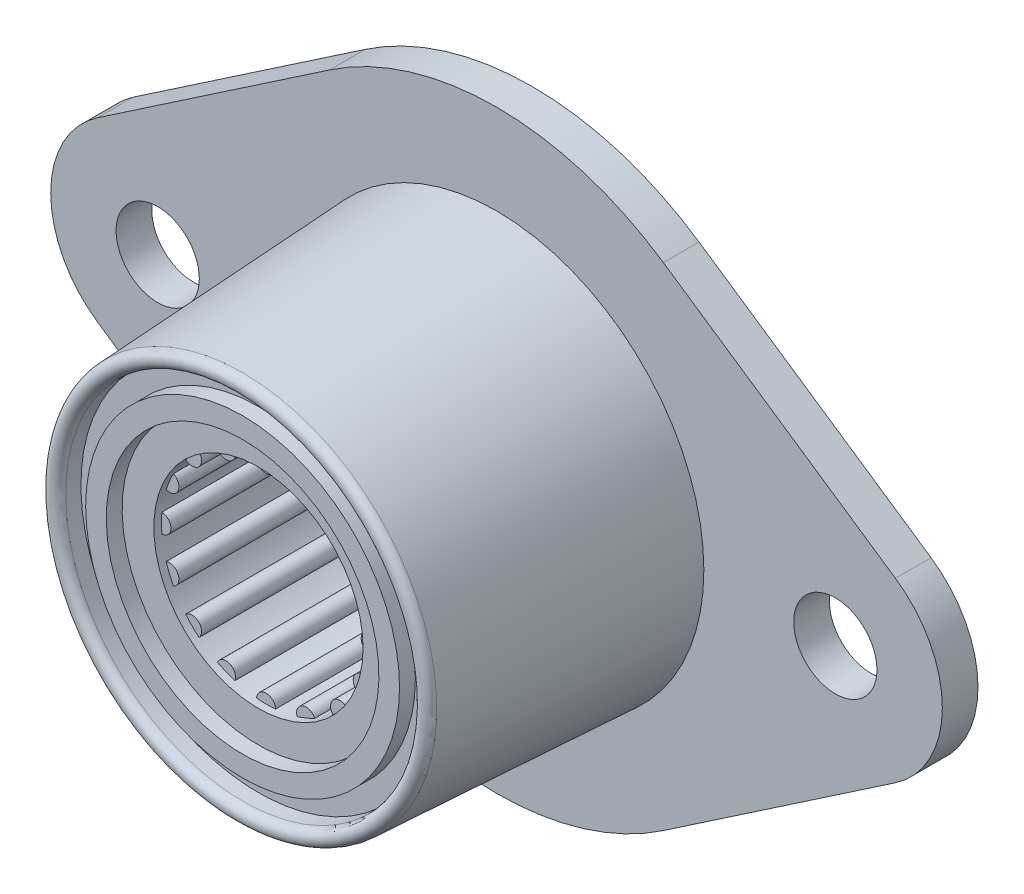
SolidWorks part; units mm, degrees
ref_plane "Front" through (0, 0, 0) normal (0, 0, 1) x (1, 0, 0)
ref_plane "Top" through (0, 0, 0) normal (0, 1, 0) x (1, 0, 0)
ref_plane "Right" through (0, 0, 0) normal (1, 0, 0) x (0, 0, -1)
sketch "Sketch1" plane through (0, 0, 0) normal (0, 0, 1) x (1, 0, 0)
  line L0 (0, 0) -> (-22.6219, 0) construction
  line L1 (0, 0) -> (22.6219, 0) construction
  line L2 (-26.6324, 5.9118) -> (-11.1404, 16.4215)
  line L3 (11.1404, 16.4215) -> (26.6324, 5.9118)
  line L4 (26.6324, -5.9118) -> (11.1404, -16.4215)
  line L5 (-11.1404, -16.4215) -> (-26.6324, -5.9118)
  line L6 (0, 19.8438) -> (0, -19.8438) construction
  arc A0 (11.1404, 16.4215) -> (-11.1404, 16.4215) centre (0, 0) ccw
  circle A1 centre (-22.6219, 0) radius 2.7781
  circle A2 centre (22.6219, 0) radius 2.7781
  arc A3 (26.6324, -5.9118) -> (26.6324, 5.9118) centre (22.6219, 0) ccw
  arc A4 (-26.6324, 5.9118) -> (-26.6324, -5.9118) centre (-22.6219, 0) ccw
  circle A5 centre (0, 0) radius 13.843
  arc A7 (-11.1404, -16.4215) -> (11.1404, -16.4215) centre (0, 0) ccw
  point P17 (0, 0)
  dimension "A" = 27.686
  dimension "Mounting Hole Dia" = 5.5562
  dimension "Overall Length" = 59.5312
  dimension "Mounting Holes" = 45.2437
  dimension "Overall Height" = 39.6875
extrude "Extrude1" add sketch "Sketch1" along normal blind 2.3813
sketch "Sketch2" plane through (0, 0, 0) normal (1, 0, 0) x (0, 0, -1)
  line L0 (0, 13.843) -> (-2.3813, 13.843)
  line L1 (-2.3813, 13.843) -> (-19.3218, 12.9552)
  line L2 (-19.2929, 11.8543) -> (-18.2769, 11.8543)
  line L3 (-18.2769, 11.8543) -> (-18.2769, 10.4782)
  line L4 (-18.2769, 6.35) -> (0, 6.35)
  line L5 (0, 6.35) -> (0, 13.843)
  line L6 (-18.2769, 10.4782) -> (-19.3357, 10.4782)
  line L7 (-19.3357, 10.4782) -> (-19.3357, 9.1022)
  line L8 (-19.3357, 9.1022) -> (-18.2769, 9.1022)
  line L9 (-18.2769, 10.4782) -> (-18.2769, 9.1022) construction
  line L10 (0, 0) -> (-18.2769, 0) construction
  line L11 (-18.2769, 0) -> (-18.2769, 6.35) construction
  line L12 (-18.2769, 7.7261) -> (-18.2769, 6.35)
  line L13 (-18.2769, 9.1022) -> (-18.2769, 7.7261)
  line L14 (0, 16.4215) -> (0, 19.8438) construction
  line L15 (0, 16.4215) -> (0, 19.8438) construction
  line L16 (-19.2929, 12.4051) -> (-19.8438, 12.4051) construction
  arc A0 (-19.3218, 12.9552) -> (-19.8438, 12.4051) centre (-19.2929, 12.4051) ccw
  arc A1 (-19.8438, 12.4051) -> (-19.2929, 11.8543) centre (-19.2929, 12.4051) ccw
  dimension "F" = 19.8438
  dimension "Shaft Dia" = 12.7
  dimension "D3" = 1.1009
  dimension "D4" = 1.016
  dimension "D5" = 3
  dimension "D2" = 0.508
  dimension "D6" = 1.3761
revolve "Revolve1" add sketch "Sketch2" angle 360 about L10
sketch "Sketch3" plane through (0, 0, 18.2769) normal (0, 0, 1) x (1, 0, 0)
  line L0 (0, 0) -> (6.985, 0) construction
  arc A0 (-3.2481, 6.1839) -> (-4.4702, 5.3673) centre (0, 0) ccw
  arc A1 (6.9561, 0.6343) -> (6.9561, -0.6343) centre (6.985, 0) ccw
  circle A2 centre (0, 0) radius 6.35 construction
  arc A3 (6.6694, -2.0759) -> (6.1839, -3.2481) centre (6.4533, -2.673) ccw
  arc A4 (5.3673, -4.4702) -> (4.4702, -5.3673) centre (4.9391, -4.9391) ccw
  arc A5 (3.2481, -6.1839) -> (2.0759, -6.6694) centre (2.673, -6.4533) ccw
  arc A6 (0.6343, -6.9561) -> (-0.6343, -6.9561) centre (0, -6.985) ccw
  arc A7 (-2.0759, -6.6694) -> (-3.2481, -6.1839) centre (-2.673, -6.4533) ccw
  arc A8 (-4.4702, -5.3673) -> (-5.3673, -4.4702) centre (-4.9391, -4.9391) ccw
  arc A9 (-6.1839, -3.2481) -> (-6.6694, -2.0759) centre (-6.4533, -2.673) ccw
  arc A10 (-6.9561, -0.6343) -> (-6.9561, 0.6343) centre (-6.985, 0) ccw
  arc A11 (-6.6694, 2.0759) -> (-6.1839, 3.2481) centre (-6.4533, 2.673) ccw
  arc A12 (-5.3673, 4.4702) -> (-4.4702, 5.3673) centre (-4.9391, 4.9391) ccw
  arc A13 (-3.2481, 6.1839) -> (-2.0759, 6.6694) centre (-2.673, 6.4533) ccw
  arc A14 (-0.6343, 6.9561) -> (0.6343, 6.9561) centre (0, 6.985) ccw
  arc A15 (2.0759, 6.6694) -> (3.2481, 6.1839) centre (2.673, 6.4533) ccw
  arc A16 (4.4702, 5.3673) -> (5.3673, 4.4702) centre (4.9391, 4.9391) ccw
  arc A17 (6.1839, 3.2481) -> (6.6694, 2.0759) centre (6.4533, 2.673) ccw
  arc A18 (-5.3673, 4.4702) -> (-6.1839, 3.2481) centre (0, 0) ccw
  arc A19 (-6.6694, 2.0759) -> (-6.9561, 0.6343) centre (0, 0) ccw
  arc A20 (-6.9561, -0.6343) -> (-6.6694, -2.0759) centre (0, 0) ccw
  arc A21 (-6.1839, -3.2481) -> (-5.3673, -4.4702) centre (0, 0) ccw
  arc A22 (-4.4702, -5.3673) -> (-3.2481, -6.1839) centre (0, 0) ccw
  arc A23 (-2.0759, -6.6694) -> (-0.6343, -6.9561) centre (0, 0) ccw
  arc A24 (0.6343, -6.9561) -> (2.0759, -6.6694) centre (0, 0) ccw
  arc A25 (3.2481, -6.1839) -> (4.4702, -5.3673) centre (0, 0) ccw
  arc A26 (5.3673, -4.4702) -> (6.1839, -3.2481) centre (0, 0) ccw
  arc A27 (6.6694, -2.0759) -> (6.9561, -0.6343) centre (0, 0) ccw
  arc A28 (6.9561, 0.6343) -> (6.6694, 2.0759) centre (0, 0) ccw
  arc A29 (6.1839, 3.2481) -> (5.3673, 4.4702) centre (0, 0) ccw
  arc A30 (4.4702, 5.3673) -> (3.2481, 6.1839) centre (0, 0) ccw
  arc A31 (2.0759, 6.6694) -> (0.6343, 6.9561) centre (0, 0) ccw
  arc A32 (-0.6343, 6.9561) -> (-2.0759, 6.6694) centre (0, 0) ccw
  dimension "D1" = 13.97
extrude "Cut-Extrude2" cut sketch "Sketch3" against normal through all
sketch "Sketch4" plane through (0, 0, 18.2769) normal (0, 0, 1) x (1, 0, 0)
  circle A0 centre (0, 0) radius 6.985
extrude "Cut-Extrude3" cut sketch "Sketch4" against normal blind 0.508
sketch "Sketch5" plane through (0, 0, 0) normal (0, 0, -1) x (-1, 0, 0)
  circle A0 centre (0, 0) radius 6.985
  arc A1 (2.0759, 6.6694) -> (0.6343, 6.9561) centre (0, 0) ccw construction
extrude "Cut-Extrude4" cut sketch "Sketch5" against normal blind 0.508
equation "\"D1@Sketch3\"=\"Shaft Dia@Sketch2\"*1.1"
equation "\"D3@Sketch2\"=\"D6@Sketch2\"/1.25"
